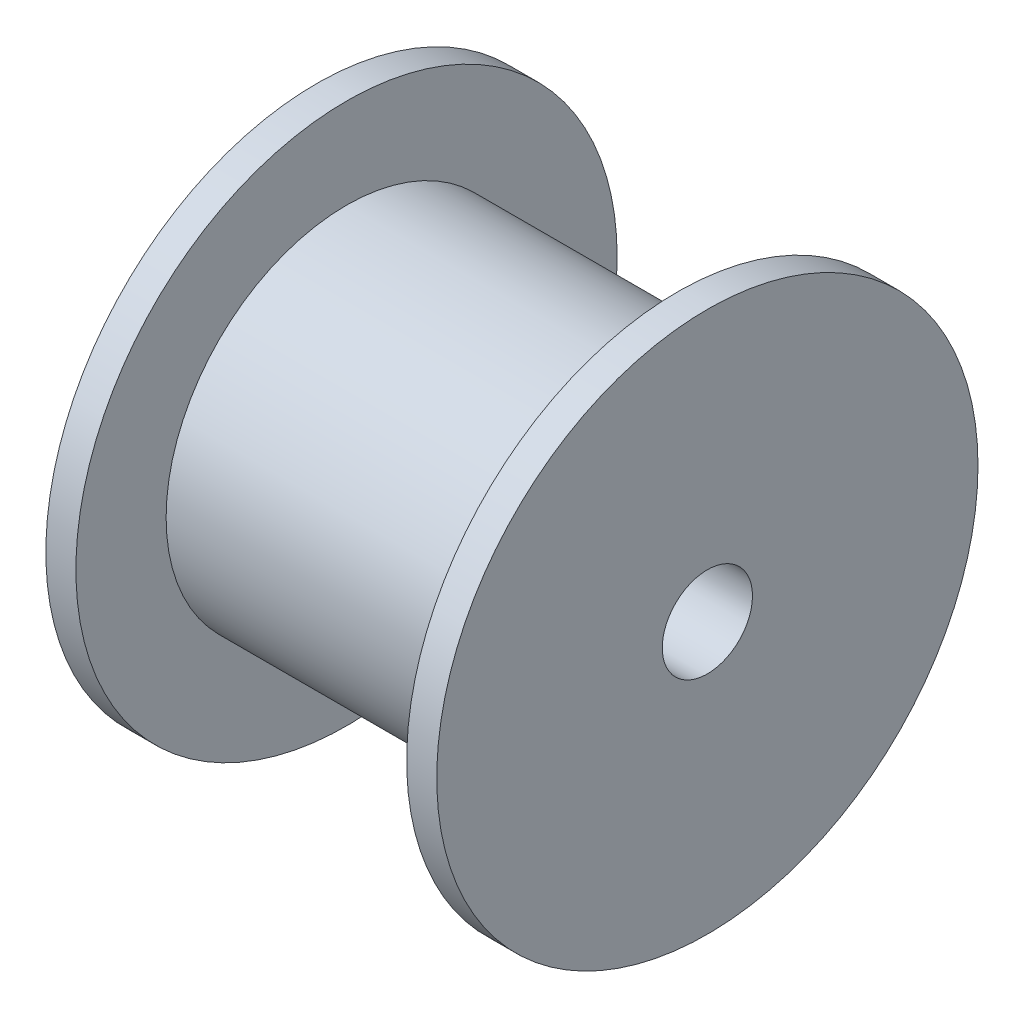
SolidWorks part; units mm, degrees
ref_plane "Front Plane" through (0, 0, 0) normal (0, 0, 1) x (1, 0, 0)
ref_plane "Top Plane" through (0, 0, 0) normal (0, 1, 0) x (1, 0, 0)
ref_plane "Right Plane" through (0, 0, 0) normal (1, 0, 0) x (0, 0, -1)
sketch "Sketch1" plane through (0, 0, 0) normal (1, 0, 0) x (0, 0, -1)
  circle A0 centre (0, 0) radius 9
  circle A1 centre (0, 0) radius 1.5
  dimension "D1" = 3
  dimension "D2" = 18
extrude "Boss-Extrude1" add sketch "Sketch1" along normal blind 1
sketch "Sketch2" plane through (1, 0, 0) normal (1, 0, 0) x (0, 0, -1)
  circle A0 centre (0, 0) radius 1.5 construction
  circle A1 centre (0, 0) radius 1.5
  circle A2 centre (0, 0) radius 6
  dimension "D1" = 12
extrude "Boss-Extrude2" add sketch "Sketch2" along normal blind 11
sketch "Sketch3" plane through (12, 0, 0) normal (1, 0, 0) x (0, 0, -1)
  circle A1 centre (0, 0) radius 1.5
  circle A2 centre (0, 0) radius 1.5
  circle A3 centre (0, 0) radius 9
  circle A4 centre (0, 0) radius 9
  dimension "D1" = 0
  dimension "D2" = 0
extrude "Boss-Extrude3" add sketch "Sketch3" along normal blind 1
